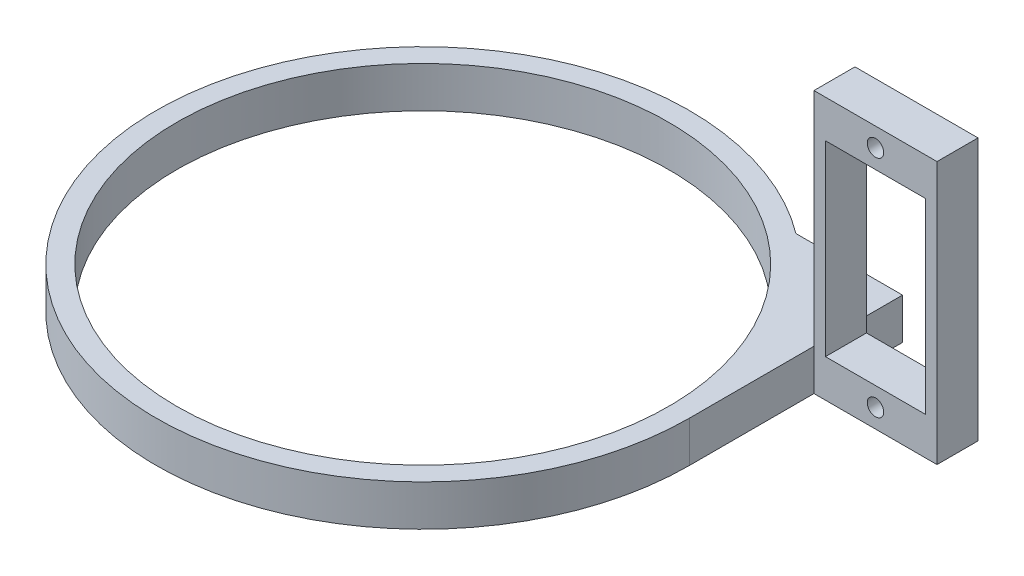
SolidWorks part; units mm, degrees
ref_plane "Front Plane" through (0, 0, 0) normal (0, 0, 1) x (1, 0, 0)
ref_plane "Top Plane" through (0, 0, 0) normal (0, 1, 0) x (1, 0, 0)
ref_plane "Right Plane" through (0, 0, 0) normal (1, 0, 0) x (0, 0, -1)
sketch "Sketch1" plane through (0, 0, 0) normal (0, 1, 0) x (1, 0, 0)
  line L0 (32.5, 0) -> (32.5, 26)
  line L1 (32.5, 26) -> (19.5, 26)
  circle A0 centre (0, 0) radius 30
  arc A1 (19.5, 26) -> (32.5, 0) centre (0, 0) ccw
  dimension "D1" = 60
  dimension "D2" = 65
  dimension "D3" = 26
extrude "Boss-Extrude1" add sketch "Sketch1" along normal blind 5
sketch "Sketch3" plane through (0, 0, 0) normal (0, 0, 1) x (1, 0, 0)
  line L0 (32.5, 0) -> (32.5, 32)
  line L1 (32.5, 32) -> (47.5, 32)
  line L2 (47.5, 32) -> (47.5, 0)
  line L3 (47.5, 0) -> (32.5, 0)
  line L4 (40, 32) -> (40, 29.7) construction
  line L5 (32.5, 16) -> (47.5, 16) construction
  line L7 (33.9, 4.6) -> (46.1, 4.6)
  line L8 (33.9, 4.6) -> (33.9, 27.4)
  line L9 (33.9, 27.4) -> (46.1, 27.4)
  line L10 (46.1, 4.6) -> (46.1, 27.4)
  line L11 (33.9, 4.6) -> (46.1, 27.4) construction
  line L12 (33.9, 27.4) -> (46.1, 4.6) construction
  circle A0 centre (40, 29.7) radius 1
  circle A1 centre (40, 2.3) radius 1
  point P12 (40, 16)
  dimension "D4" = 2
  dimension "D1" = 32
  dimension "D2" = 15
  dimension "D3" = 2.3
  dimension "D5" = 22.8
  dimension "D6" = 12.2
extrude "Boss-Extrude4" add sketch "Sketch3" along normal blind 5 from offset 20.2
